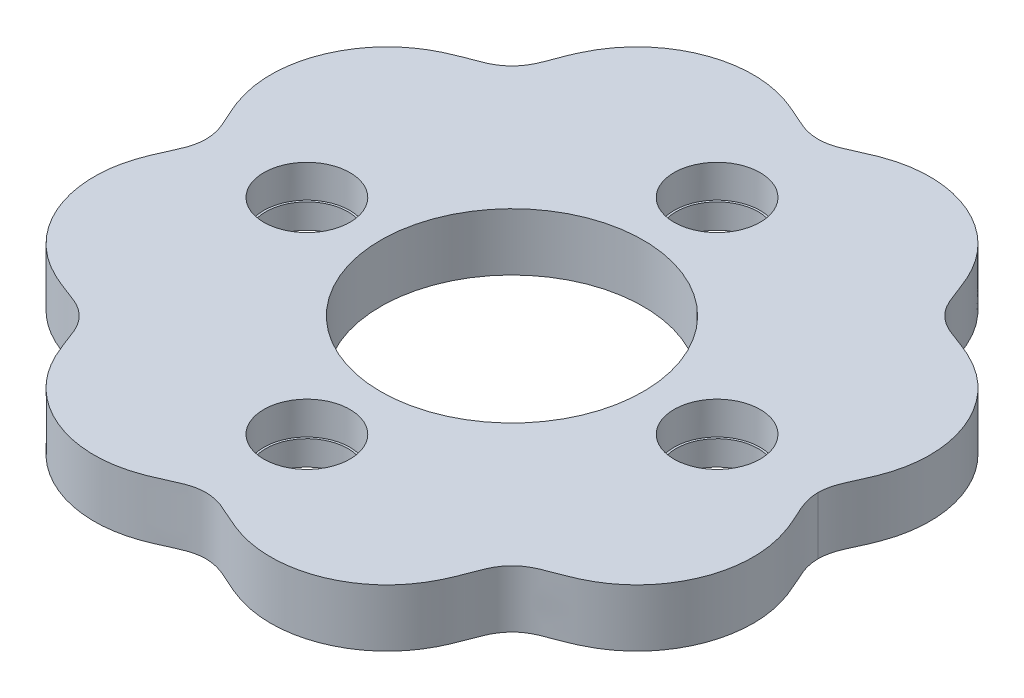
SolidWorks part; units mm, degrees
material "PET"
ref_plane "Front Plane" through (0, 0, 0) normal (0, 0, 1) x (1, 0, 0)
ref_plane "Top Plane" through (0, 0, 0) normal (0, 1, 0) x (1, 0, 0)
ref_plane "Right Plane" through (0, 0, 0) normal (1, 0, 0) x (0, 0, -1)
sketch "Sketch2" plane through (0, 0, 0) normal (0, 1, 0) x (1, 0, 0)
  line L0 (-37.5, 0) -> (37.5, 0) construction
  spline S0 degree 4 poles (36.9805, 20.0285) (37.2753, 19.6778) (37.8347, 18.9513) (38.4555, 17.9854) (39.0737, 16.7557) (39.5005, 15.6923) (39.7876, 14.8217) (40.0191, 13.9346) (40.1939, 13.0347) (40.3111, 12.1255) (40.3698, 11.2106) (40.3695, 10.2938) (40.3175, 9.4934) (40.2359, 8.8108) (40.1529, 8.3024) (40.0885, 7.9647) (40.0287, 7.6841) (39.9777, 7.4611) (39.9238, 7.2412) (39.8664, 7.0219) (39.8025, 6.7937) (39.7309, 6.5533) (39.6637, 6.3374) (39.6136, 6.1836) (39.5479, 5.991) (39.4755, 5.7851) (39.4027, 5.5855) (39.3311, 5.3965) (39.2407, 5.1663) (39.1279, 4.8896) (38.9903, 4.5651) (38.8283, 4.1989) (38.6621, 3.8341) (38.4352, 3.3438) (38.1502, 2.7272) (37.8212, 1.946) (37.5468, 0.9653) (37.4535, -0.0911) (37.5698, -1.0461) (37.7995, -1.8451) (38.0553, -2.5006) (38.2844, -3.0188) (38.5476, -3.5861) (38.8343, -4.2072) (39.213, -5.0714) (39.6429, -6.1955) (40.0348, -7.5456) (40.3091, -9.1291) (40.4025, -10.7334) (40.2923, -12.7392) (39.8007, -15.1154) (38.875, -17.3723) (37.5505, -19.4168) (36.2019, -20.9371) (34.9913, -22.0223) (33.6644, -22.9618) (32.4189, -23.6484) (31.3072, -24.1448) (30.4154, -24.4925) (29.7608, -24.7333) (29.1593, -24.9537) (28.6152, -25.1661) (27.9682, -25.4558) (27.2425, -25.8692) (26.4868, -26.4785) (25.7889, -27.3386) (25.3334, -28.1996) (25.0208, -28.9789) (24.7562, -29.6972) (24.5201, -30.3421) (24.1768, -31.23) (23.6857, -32.344) (23.006, -33.5933) (22.0744, -34.9257) (20.9963, -36.1426) (19.484, -37.5001) (17.4364, -38.8435) (15.1658, -39.787) (12.7656, -40.2907) (10.7279, -40.4037) (9.0981, -40.3067) (7.4903, -40.0231) (6.1205, -39.6185) (4.9809, -39.1759) (3.9811, -38.7332) (3.1077, -38.3232) (2.1628, -37.8962) (1.1027, -37.5687) (0, -37.4517) (-1.1027, -37.5687) (-2.1628, -37.8962) (-3.1077, -38.3232) (-3.9811, -38.7332) (-4.9809, -39.1759) (-6.1205, -39.6185) (-7.4903, -40.0231) (-9.0981, -40.3067) (-10.7279, -40.4037) (-12.7656, -40.2907) (-15.1658, -39.787) (-17.4364, -38.8435) (-19.484, -37.5001) (-20.9963, -36.1426) (-22.0744, -34.9257) (-23.006, -33.5933) (-23.6856, -32.3439) (-24.1768, -31.23) (-24.5707, -30.2109) (-24.8996, -29.3004) (-25.2674, -28.3245) (-25.7889, -27.3386) (-26.4868, -26.4785) (-27.2424, -25.8692) (-27.9682, -25.4558) (-28.6151, -25.166) (-29.1593, -24.9537) (-29.7608, -24.7333) (-30.4154, -24.4925) (-31.3072, -24.1448) (-32.4189, -23.6484) (-33.6644, -22.9618) (-34.9913, -22.0223) (-36.2019, -20.9371) (-37.5505, -19.4168) (-38.875, -17.3723) (-39.8007, -15.1154) (-40.2923, -12.7392) (-40.4025, -10.7334) (-40.3091, -9.1291) (-40.0348, -7.5456) (-39.6429, -6.1955) (-39.213, -5.0714) (-38.8343, -4.2072) (-38.5476, -3.5861) (-38.2844, -3.0188) (-38.0553, -2.5006) (-37.7995, -1.8451) (-37.5698, -1.0461) (-37.4535, -0.0911) (-37.5468, 0.9653) (-37.8212, 1.946) (-38.1502, 2.7272) (-38.4352, 3.3438) (-38.6621, 3.8341) (-38.8283, 4.1989) (-38.9903, 4.5651) (-39.1279, 4.8896) (-39.2407, 5.1663) (-39.3311, 5.3965) (-39.4027, 5.5855) (-39.4755, 5.7851) (-39.5479, 5.991) (-39.6136, 6.1836) (-39.6637, 6.3374) (-39.7309, 6.5533) (-39.8025, 6.7937) (-39.8664, 7.0219) (-39.9238, 7.2412) (-39.9777, 7.4611) (-40.0287, 7.6841) (-40.0885, 7.9647) (-40.1529, 8.3024) (-40.2359, 8.8108) (-40.3175, 9.4934) (-40.3695, 10.2938) (-40.3698, 11.2106) (-40.3111, 12.1255) (-40.1939, 13.0347) (-40.0191, 13.9346) (-39.7876, 14.8217) (-39.5005, 15.6923) (-39.0737, 16.7557) (-38.4555, 17.9854) (-37.8347, 18.9513) (-37.2753, 19.6778) (-36.9805, 20.0285) knots 0 0 0 0 0 0.010311 0.020621 0.025777 0.030932 0.036087 0.041243 0.046398 0.051553 0.056709 0.061864 0.067019 0.069597 0.072175 0.073463 0.074752 0.076041 0.07733 0.078618 0.079907 0.081196 0.082485 0.083613 0.084741 0.085869 0.086997 0.088125 0.089253 0.091509 0.093765 0.09602 0.098276 0.100532 0.105923 0.111314 0.117336 0.123359 0.129627 0.132815 0.136003 0.139191 0.142379 0.146891 0.151403 0.160427 0.169451 0.178475 0.1875 0.196524 0.214573 0.232831 0.24196 0.251089 0.260218 0.269348 0.278476 0.28304 0.287605 0.29089 0.294176 0.297462 0.300748 0.306838 0.312927 0.319161 0.325494 0.32866 0.331826 0.33639 0.340955 0.350083 0.359212 0.368341 0.37747 0.386599 0.404858 0.423193 0.432361 0.441528 0.450696 0.459863 0.46903 0.473614 0.478197 0.484473 0.490748 0.496943 0.503057 0.509252 0.515527 0.521803 0.526386 0.53097 0.540137 0.549304 0.558472 0.567639 0.576807 0.595142 0.613401 0.62253 0.631659 0.640788 0.649917 0.659045 0.66361 0.668174 0.674506 0.680839 0.687073 0.693162 0.699252 0.702538 0.705824 0.70911 0.712395 0.71696 0.721524 0.730652 0.739782 0.748911 0.75804 0.767169 0.785427 0.803476 0.8125 0.821525 0.830549 0.839573 0.848597 0.853109 0.857621 0.860809 0.863997 0.867185 0.870373 0.876641 0.882664 0.888686 0.894077 0.899468 0.901724 0.90398 0.906235 0.908491 0.910747 0.911875 0.913003 0.914131 0.915259 0.916387 0.917515 0.918804 0.920093 0.921382 0.92267 0.923959 0.925248 0.926537 0.927825 0.930403 0.932981 0.938136 0.943291 0.948447 0.953602 0.958757 0.963913 0.969068 0.974223 0.979379 0.989689 1 1 1 1 1 construction
  spline S1 degree 4 poles (37.5, 0) (37.5, -0.1537) (37.5167, -0.5857) (37.6013, -1.1559) (37.7995, -1.8451) (38.0553, -2.5006) (38.2844, -3.0188) (38.5476, -3.5861) (38.8343, -4.2072) (39.213, -5.0714) (39.6429, -6.1955) (40.0348, -7.5456) (40.3091, -9.1291) (40.4025, -10.7334) (40.2923, -12.7392) (39.8007, -15.1154) (38.875, -17.3723) (37.5505, -19.4168) (36.2019, -20.9371) (34.9913, -22.0223) (33.6644, -22.9618) (32.4189, -23.6484) (31.3072, -24.1448) (30.4154, -24.4925) (29.7608, -24.7333) (29.1593, -24.9537) (28.6152, -25.1661) (27.9682, -25.4558) (27.2425, -25.8692) (26.4868, -26.4785) (25.7889, -27.3386) (25.3334, -28.1996) (25.0208, -28.9789) (24.7562, -29.6972) (24.5201, -30.3421) (24.1768, -31.23) (23.6857, -32.344) (23.006, -33.5933) (22.0744, -34.9257) (20.9963, -36.1426) (19.484, -37.5001) (17.4364, -38.8435) (15.1658, -39.787) (12.7656, -40.2907) (10.7279, -40.4037) (9.0981, -40.3067) (7.4903, -40.0231) (6.1205, -39.6185) (4.9809, -39.1759) (3.9811, -38.7332) (3.1077, -38.3232) (2.1628, -37.8962) (1.1027, -37.5687) (0, -37.4517) (-1.1027, -37.5687) (-2.1628, -37.8962) (-3.1077, -38.3232) (-3.9811, -38.7332) (-4.9809, -39.1759) (-6.1205, -39.6185) (-7.4903, -40.0231) (-9.0981, -40.3067) (-10.7279, -40.4037) (-12.7656, -40.2907) (-15.1658, -39.787) (-17.4364, -38.8435) (-19.484, -37.5001) (-20.9963, -36.1426) (-22.0744, -34.9257) (-23.006, -33.5933) (-23.6856, -32.3439) (-24.1768, -31.23) (-24.5707, -30.2109) (-24.8996, -29.3004) (-25.2674, -28.3245) (-25.7889, -27.3386) (-26.4868, -26.4785) (-27.2424, -25.8692) (-27.9682, -25.4558) (-28.6151, -25.166) (-29.1593, -24.9537) (-29.7608, -24.7333) (-30.4154, -24.4925) (-31.3072, -24.1448) (-32.4189, -23.6484) (-33.6644, -22.9618) (-34.9913, -22.0223) (-36.2019, -20.9371) (-37.5505, -19.4168) (-38.875, -17.3723) (-39.8007, -15.1154) (-40.2923, -12.7392) (-40.4025, -10.7334) (-40.3091, -9.1291) (-40.0348, -7.5456) (-39.6429, -6.1955) (-39.213, -5.0714) (-38.8343, -4.2072) (-38.5476, -3.5861) (-38.2844, -3.0188) (-38.0553, -2.5006) (-37.7995, -1.8451) (-37.6013, -1.1559) (-37.5167, -0.5857) (-37.5, -0.1537) (-37.5, 0) knots 0.119901 0.119901 0.119901 0.119901 0.119901 0.123359 0.129627 0.132815 0.136003 0.139191 0.142379 0.146891 0.151403 0.160427 0.169451 0.178475 0.1875 0.196524 0.214573 0.232831 0.24196 0.251089 0.260218 0.269348 0.278476 0.28304 0.287605 0.29089 0.294176 0.297462 0.300748 0.306838 0.312927 0.319161 0.325494 0.32866 0.331826 0.33639 0.340955 0.350083 0.359212 0.368341 0.37747 0.386599 0.404858 0.423193 0.432361 0.441528 0.450696 0.459863 0.46903 0.473614 0.478197 0.484473 0.490748 0.496943 0.503057 0.509252 0.515527 0.521803 0.526386 0.53097 0.540137 0.549304 0.558472 0.567639 0.576807 0.595142 0.613401 0.62253 0.631659 0.640788 0.649917 0.659045 0.66361 0.668174 0.674506 0.680839 0.687073 0.693162 0.699252 0.702538 0.705824 0.70911 0.712395 0.71696 0.721524 0.730652 0.739782 0.748911 0.75804 0.767169 0.785427 0.803476 0.8125 0.821525 0.830549 0.839573 0.848597 0.853109 0.857621 0.860809 0.863997 0.867185 0.870373 0.876641 0.880099 0.880099 0.880099 0.880099 0.880099
  spline S2 degree 4 poles (37.5, 0) (37.5, 0.1537) (37.5167, 0.5857) (37.6013, 1.1559) (37.7995, 1.8451) (38.0553, 2.5006) (38.2844, 3.0188) (38.5476, 3.5861) (38.8343, 4.2072) (39.213, 5.0714) (39.6429, 6.1955) (40.0348, 7.5456) (40.3091, 9.1291) (40.4025, 10.7334) (40.2923, 12.7392) (39.8007, 15.1154) (38.875, 17.3723) (37.5505, 19.4168) (36.2019, 20.9371) (34.9913, 22.0223) (33.6644, 22.9618) (32.4189, 23.6484) (31.3072, 24.1448) (30.4154, 24.4925) (29.7608, 24.7333) (29.1593, 24.9537) (28.6152, 25.1661) (27.9682, 25.4558) (27.2425, 25.8692) (26.4868, 26.4785) (25.7889, 27.3386) (25.3334, 28.1996) (25.0208, 28.9789) (24.7562, 29.6972) (24.5201, 30.3421) (24.1768, 31.23) (23.6857, 32.344) (23.006, 33.5933) (22.0744, 34.9257) (20.9963, 36.1426) (19.484, 37.5001) (17.4364, 38.8435) (15.1658, 39.787) (12.7656, 40.2907) (10.7279, 40.4037) (9.0981, 40.3067) (7.4903, 40.0231) (6.1205, 39.6185) (4.9809, 39.1759) (3.9811, 38.7332) (3.1077, 38.3232) (2.1628, 37.8962) (1.1027, 37.5687) (0, 37.4517) (-1.1027, 37.5687) (-2.1628, 37.8962) (-3.1077, 38.3232) (-3.9811, 38.7332) (-4.9809, 39.1759) (-6.1205, 39.6185) (-7.4903, 40.0231) (-9.0981, 40.3067) (-10.7279, 40.4037) (-12.7656, 40.2907) (-15.1658, 39.787) (-17.4364, 38.8435) (-19.484, 37.5001) (-20.9963, 36.1426) (-22.0744, 34.9257) (-23.006, 33.5933) (-23.6856, 32.3439) (-24.1768, 31.23) (-24.5707, 30.2109) (-24.8996, 29.3004) (-25.2674, 28.3245) (-25.7889, 27.3386) (-26.4868, 26.4785) (-27.2424, 25.8692) (-27.9682, 25.4558) (-28.6151, 25.166) (-29.1593, 24.9537) (-29.7608, 24.7333) (-30.4154, 24.4925) (-31.3072, 24.1448) (-32.4189, 23.6484) (-33.6644, 22.9618) (-34.9913, 22.0223) (-36.2019, 20.9371) (-37.5505, 19.4168) (-38.875, 17.3723) (-39.8007, 15.1154) (-40.2923, 12.7392) (-40.4025, 10.7334) (-40.3091, 9.1291) (-40.0348, 7.5456) (-39.6429, 6.1955) (-39.213, 5.0714) (-38.8343, 4.2072) (-38.5476, 3.5861) (-38.2844, 3.0188) (-38.0553, 2.5006) (-37.7995, 1.8451) (-37.6013, 1.1559) (-37.5167, 0.5857) (-37.5, 0.1537) (-37.5, 0) knots 0.119901 0.119901 0.119901 0.119901 0.119901 0.123359 0.129627 0.132815 0.136003 0.139191 0.142379 0.146891 0.151403 0.160427 0.169451 0.178475 0.1875 0.196524 0.214573 0.232831 0.24196 0.251089 0.260218 0.269348 0.278476 0.28304 0.287605 0.29089 0.294176 0.297462 0.300748 0.306838 0.312927 0.319161 0.325494 0.32866 0.331826 0.33639 0.340955 0.350083 0.359212 0.368341 0.37747 0.386599 0.404858 0.423193 0.432361 0.441528 0.450696 0.459863 0.46903 0.473614 0.478197 0.484473 0.490748 0.496943 0.503057 0.509252 0.515527 0.521803 0.526386 0.53097 0.540137 0.549304 0.558472 0.567639 0.576807 0.595142 0.613401 0.62253 0.631659 0.640788 0.649917 0.659045 0.66361 0.668174 0.674506 0.680839 0.687073 0.693162 0.699252 0.702538 0.705824 0.70911 0.712395 0.71696 0.721524 0.730652 0.739782 0.748911 0.75804 0.767169 0.785427 0.803476 0.8125 0.821525 0.830549 0.839573 0.848597 0.853109 0.857621 0.860809 0.863997 0.867185 0.870373 0.876641 0.880099 0.880099 0.880099 0.880099 0.880099
extrude "Boss-Extrude1" add sketch "Sketch2" along normal blind 7 contours S2 S1
sketch "Sketch3" plane through (0, 7, 0) normal (0, 1, 0) x (1, 0, 0)
  line L0 (0, 0) -> (37.5, 0) construction
  circle A0 centre (0, 0) radius 16
  circle A1 centre (25, 0) radius 5.25
  circle A3 centre (0, -25) radius 5.25
  circle A4 centre (-25, 0) radius 5.25
  circle A5 centre (0, 25) radius 5.25
  spline S0 degree 4 poles (37.5, 0) (37.5, -0.1537) (37.5167, -0.5857) (37.6013, -1.1559) (37.7995, -1.8451) (38.0553, -2.5006) (38.2844, -3.0188) (38.5476, -3.5861) (38.8343, -4.2072) (39.213, -5.0714) (39.6429, -6.1955) (40.0348, -7.5456) (40.3091, -9.1291) (40.4025, -10.7334) (40.2923, -12.7392) (39.8007, -15.1154) (38.875, -17.3723) (37.5505, -19.4168) (36.2019, -20.9371) (34.9913, -22.0223) (33.6644, -22.9618) (32.4189, -23.6484) (31.3072, -24.1448) (30.4154, -24.4925) (29.7608, -24.7333) (29.1593, -24.9537) (28.6152, -25.1661) (27.9682, -25.4558) (27.2425, -25.8692) (26.4868, -26.4785) (25.7889, -27.3386) (25.3334, -28.1996) (25.0208, -28.9789) (24.7562, -29.6972) (24.5201, -30.3421) (24.1768, -31.23) (23.6857, -32.344) (23.006, -33.5933) (22.0744, -34.9257) (20.9963, -36.1426) (19.484, -37.5001) (17.4364, -38.8435) (15.1658, -39.787) (12.7656, -40.2907) (10.7279, -40.4037) (9.0981, -40.3067) (7.4903, -40.0231) (6.1205, -39.6185) (4.9809, -39.1759) (3.9811, -38.7332) (3.1077, -38.3232) (2.1628, -37.8962) (1.1027, -37.5687) (0, -37.4517) (-1.1027, -37.5687) (-2.1628, -37.8962) (-3.1077, -38.3232) (-3.9811, -38.7332) (-4.9809, -39.1759) (-6.1205, -39.6185) (-7.4903, -40.0231) (-9.0981, -40.3067) (-10.7279, -40.4037) (-12.7656, -40.2907) (-15.1658, -39.787) (-17.4364, -38.8435) (-19.484, -37.5001) (-20.9963, -36.1426) (-22.0744, -34.9257) (-23.006, -33.5933) (-23.6856, -32.3439) (-24.1768, -31.23) (-24.5707, -30.2109) (-24.8996, -29.3004) (-25.2674, -28.3245) (-25.7889, -27.3386) (-26.4868, -26.4785) (-27.2424, -25.8692) (-27.9682, -25.4558) (-28.6151, -25.166) (-29.1593, -24.9537) (-29.7608, -24.7333) (-30.4154, -24.4925) (-31.3072, -24.1448) (-32.4189, -23.6484) (-33.6644, -22.9618) (-34.9913, -22.0223) (-36.2019, -20.9371) (-37.5505, -19.4168) (-38.875, -17.3723) (-39.8007, -15.1154) (-40.2923, -12.7392) (-40.4025, -10.7334) (-40.3091, -9.1291) (-40.0348, -7.5456) (-39.6429, -6.1955) (-39.213, -5.0714) (-38.8343, -4.2072) (-38.5476, -3.5861) (-38.2844, -3.0188) (-38.0553, -2.5006) (-37.7995, -1.8451) (-37.6013, -1.1559) (-37.5167, -0.5857) (-37.5, -0.1537) (-37.5, 0) knots 0.119901 0.119901 0.119901 0.119901 0.119901 0.123359 0.129627 0.132815 0.136003 0.139191 0.142379 0.146891 0.151403 0.160427 0.169451 0.178475 0.1875 0.196524 0.214573 0.232831 0.24196 0.251089 0.260218 0.269348 0.278476 0.28304 0.287605 0.29089 0.294176 0.297462 0.300748 0.306838 0.312927 0.319161 0.325494 0.32866 0.331826 0.33639 0.340955 0.350083 0.359212 0.368341 0.37747 0.386599 0.404858 0.423193 0.432361 0.441528 0.450696 0.459863 0.46903 0.473614 0.478197 0.484473 0.490748 0.496943 0.503057 0.509252 0.515527 0.521803 0.526386 0.53097 0.540137 0.549304 0.558472 0.567639 0.576807 0.595142 0.613401 0.62253 0.631659 0.640788 0.649917 0.659045 0.66361 0.668174 0.674506 0.680839 0.687073 0.693162 0.699252 0.702538 0.705824 0.70911 0.712395 0.71696 0.721524 0.730652 0.739782 0.748911 0.75804 0.767169 0.785427 0.803476 0.8125 0.821525 0.830549 0.839573 0.848597 0.853109 0.857621 0.860809 0.863997 0.867185 0.870373 0.876641 0.880099 0.880099 0.880099 0.880099 0.880099 construction
  point P8 (37.5, 0)
  point P18 (0, 0)
  dimension "D1" = 32
  dimension "D2" = 10.5
  dimension "D4" = 25
  dimension "D5" = 4
extrude "Cut-Extrude1" cut sketch "Sketch3" against normal blind 7
sketch "Sketch4" plane through (0, 0, 0) normal (0, -1, 0) x (1, 0, 0)
  spline S4 degree 3 poles (-2948.3885, 722.0287) (-151.4363, 76.2208) (-29.3122, 22.69) (-37.8533, -2.585) (-38.1471, -3.1952) (-38.7107, -4.4187) (-38.9828, -5.0336) (-39.4508, -6.2882) (-39.648, -6.9276) (-39.8757, -7.9088) (-39.9403, -8.2396) (-40.0461, -8.9088) (-40.0873, -9.2487) (-40.1729, -10.2702) (-40.1796, -10.9476) (-40.0964, -12.2955) (-40.0066, -12.966) (-39.7983, -13.9664) (-39.7162, -14.2999) (-39.5299, -14.9551) (-39.4254, -15.2779) (-39.079, -16.2318) (-38.8042, -16.8488) (-38.1662, -18.0446) (-37.7995, -18.6276) (-36.9951, -19.7223) (-36.557, -20.2365) (-35.6094, -21.1989) (-35.0988, -21.6477) (-34.0068, -22.4733) (-33.4366, -22.8413) (-32.2526, -23.4966) (-31.6381, -23.7828) (-30.6936, -24.1698) (-30.3749, -24.292) (-29.7353, -24.5302) (-29.4141, -24.6459) (-28.7761, -24.8878) (-28.4596, -25.0146) (-27.8419, -25.305) (-27.5385, -25.4704) (-26.9685, -25.8482) (-26.7027, -26.0593) (-26.2122, -26.5296) (-25.9857, -26.7918) (-25.5865, -27.3477) (-25.4133, -27.6409) (-25.1061, -28.2501) (-24.9721, -28.5662) (-24.722, -29.2071) (-24.6047, -29.5314) (-24.366, -30.178) (-24.2449, -30.5004) (-23.862, -31.4579) (-23.58, -32.0828) (-22.9307, -33.2897) (-22.5646, -33.8723) (-21.9447, -34.7109) (-21.7254, -34.9856) (-21.2703, -35.5135) (-21.0341, -35.7676) (-20.2998, -36.5011) (-19.7765, -36.9518) (-18.6627, -37.777) (-18.0672, -38.1536) (-16.8421, -38.8083) (-16.2104, -39.0887) (-15.2346, -39.4401) (-14.9046, -39.5456) (-14.235, -39.7331) (-13.894, -39.8152) (-12.1831, -40.161) (-10.8043, -40.2342) (-9.068, -40.0667) (-8.72, -40.0198) (-8.034, -39.9014) (-7.6946, -39.8297) (-6.6868, -39.5791) (-6.0289, -39.3634) (-4.7349, -38.8569) (-4.0997, -38.5639) (-2.8312, -37.9786) (-2.1955, -37.6898) (-1.1773, -37.4157) (-0.8309, -37.3518) (-0.1388, -37.2909) (0.2091, -37.2929) (0.9087, -37.3638) (1.2541, -37.4328) (1.9235, -37.621) (2.2502, -37.7405) (2.8946, -38.0077) (3.2126, -38.1544) (3.8487, -38.4482) (4.1667, -38.5954) (5.126, -39.018) (5.773, -39.274) (7.0935, -39.6938) (7.7666, -39.859) (8.7979, -40.0311) (9.1453, -40.076) (9.8476, -40.1396) (10.2044, -40.1583) (11.9811, -40.1834) (13.3741, -39.9912) (15.0807, -39.4906) (15.419, -39.3775) (16.0811, -39.1284) (16.4062, -38.9921) (17.364, -38.5485) (17.9792, -38.2067) (18.8662, -37.6232) (19.1571, -37.416) (19.72, -36.9818) (19.9916, -36.7554) (20.7778, -36.0486) (21.2637, -35.5408) (21.9348, -34.7238) (22.1489, -34.4422) (22.5573, -33.8603) (22.7513, -33.5603) (23.2966, -32.6452) (23.6131, -32.0104) (24.035, -31.0305) (24.1671, -30.6994) (24.4207, -30.0336) (24.5422, -29.6985) (24.7899, -29.0303) (24.9163, -28.6973) (25.203, -28.0449) (25.3653, -27.7235) (25.7389, -27.1186) (25.9496, -26.8348) (26.4253, -26.3096) (26.6934, -26.0663) (27.2624, -25.6405) (27.5646, -25.4559) (28.1962, -25.1299) (28.5258, -24.9886) (29.1951, -24.726) (29.5346, -24.6036) (30.211, -24.3537) (30.5481, -24.2267) (31.5472, -23.8241) (32.1968, -23.526) (33.4451, -22.8381) (34.0446, -22.4496) (34.9029, -21.793) (35.1822, -21.5619) (35.7264, -21.0739) (35.9929, -20.8154) (36.7549, -20.0151) (37.2156, -19.4476) (38.0459, -18.2477) (38.4158, -17.6149) (39.0608, -16.2832) (39.3278, -15.6011) (39.7553, -14.2058) (39.9157, -13.4925) (40.0733, -12.3983) (40.1117, -12.0294) (40.1591, -11.2964) (40.1684, -10.9307) (40.1534, -9.836) (40.0865, -9.1093) (39.8999, -8.0241) (39.8229, -7.6619) (39.642, -6.9461) (39.5382, -6.593) (39.1911, -5.5467) (38.9098, -4.8672) (38.4549, -3.8599) (38.2979, -3.5261) (37.9924, -2.8554) (37.8446, -2.5182) (37.5906, -1.8289) (37.4849, -1.4765) (32.6595, 22.6356) (171.7208, 86.8036) (1900.9011, -2345.5194) knots -0.595862 -0.595862 -0.595862 -0.595862 0.015625 0.015625 0.03125 0.03125 0.046875 0.046875 0.0625 0.0625 0.070312 0.070312 0.078125 0.078125 0.09375 0.09375 0.109375 0.109375 0.117187 0.117187 0.125 0.125 0.140625 0.140625 0.15625 0.15625 0.171875 0.171875 0.1875 0.1875 0.203125 0.203125 0.21875 0.21875 0.226562 0.226562 0.234375 0.234375 0.242187 0.242187 0.25 0.25 0.257812 0.257812 0.265625 0.265625 0.273437 0.273437 0.28125 0.28125 0.289062 0.289062 0.296875 0.296875 0.3125 0.3125 0.328125 0.328125 0.335937 0.335937 0.34375 0.34375 0.359375 0.359375 0.375 0.375 0.390625 0.390625 0.398437 0.398437 0.40625 0.40625 0.4375 0.4375 0.445312 0.445312 0.453125 0.453125 0.46875 0.46875 0.484375 0.484375 0.5 0.5 0.507812 0.507812 0.515625 0.515625 0.523437 0.523437 0.53125 0.53125 0.539062 0.539062 0.546875 0.546875 0.5625 0.5625 0.578125 0.578125 0.585937 0.585937 0.59375 0.59375 0.625 0.625 0.632812 0.632812 0.640625 0.640625 0.65625 0.65625 0.664062 0.664062 0.671875 0.671875 0.6875 0.6875 0.695312 0.695312 0.703125 0.703125 0.71875 0.71875 0.726562 0.726562 0.734375 0.734375 0.742187 0.742187 0.75 0.75 0.757812 0.757812 0.765625 0.765625 0.773437 0.773437 0.78125 0.78125 0.789062 0.789062 0.796875 0.796875 0.8125 0.8125 0.828125 0.828125 0.835937 0.835937 0.84375 0.84375 0.859375 0.859375 0.875 0.875 0.890625 0.890625 0.90625 0.90625 0.914062 0.914062 0.921875 0.921875 0.9375 0.9375 0.945312 0.945312 0.953125 0.953125 0.96875 0.96875 0.976562 0.976562 0.984375 0.984375 0.992187 0.992187 1.5015 1.5015 1.5015 1.5015 only from (-37.3, 0) to (37.3, 0)
  spline S5 degree 3 poles (2959.6942, -674.8836) (159.4413, -76.6329) (29.2837, -23.2287) (37.8317, 2.5321) (38.1169, 3.1309) (38.67, 4.3291) (38.9391, 4.9306) (39.406, 6.1564) (39.605, 6.7803) (39.9166, 8.056) (40.0298, 8.7075) (40.1293, 9.7073) (40.1505, 10.0435) (40.1686, 10.7108) (40.1657, 11.0433) (40.1219, 12.0378) (40.046, 12.6965) (39.8009, 14.0056) (39.6299, 14.66) (39.2033, 15.9228) (38.9476, 16.535) (38.3524, 17.7213) (38.0116, 18.2974) (36.8656, 19.953) (35.9651, 20.9257) (34.6682, 21.9774) (34.3991, 22.18) (33.8491, 22.5642) (33.5682, 22.7458) (32.7084, 23.2605) (32.1122, 23.5629) (30.8834, 24.1035) (30.2535, 24.3387) (28.9923, 24.8027) (28.3593, 25.0337) (27.173, 25.6725) (26.6404, 26.0718) (25.7322, 27.0751) (25.3881, 27.6463) (24.9705, 28.5655) (24.8471, 28.881) (24.6087, 29.5163) (24.4932, 29.836) (24.1362, 30.7892) (23.8828, 31.4162) (23.0112, 33.2354) (22.2825, 34.3665) (21.1418, 35.6532) (20.9009, 35.9055) (20.4029, 36.3896) (20.1462, 36.621) (19.3542, 37.2845) (18.7968, 37.6859) (17.9172, 38.2274) (17.6167, 38.3978) (17.0008, 38.7178) (16.6853, 38.8674) (15.7319, 39.2776) (15.0821, 39.5029) (13.7545, 39.8588) (13.0763, 39.9895) (11.6925, 40.1507) (11.0033, 40.1794) (9.6304, 40.1362) (8.9466, 40.0641) (7.9251, 39.8793) (7.5841, 39.8046) (6.9111, 39.6316) (6.5788, 39.5334) (5.5932, 39.2068) (4.9518, 38.945) (4.0012, 38.5197) (3.6862, 38.3727) (3.0549, 38.0823) (2.7387, 37.939) (1.7744, 37.5551) (1.1084, 37.3657) (-0.3132, 37.2631) (-1.0098, 37.3537) (-2.3731, 37.7595) (-3.0204, 38.0657) (-4.3192, 38.6656) (-4.971, 38.9584) (-6.3033, 39.4574) (-6.9832, 39.6657) (-8.0287, 39.9006) (-8.3815, 39.9661) (-9.096, 40.0703) (-9.4592, 40.109) (-10.5423, 40.1818) (-11.2606, 40.1739) (-12.6902, 40.0495) (-13.4023, 39.9326) (-14.8151, 39.5876) (-15.4996, 39.3636) (-16.8266, 38.8168) (-17.469, 38.4941) (-18.4002, 37.9335) (-18.7053, 37.7335) (-19.294, 37.3147) (-19.5789, 37.095) (-20.4061, 36.4056) (-20.9207, 35.9057) (-21.636, 35.094) (-21.8657, 34.8121) (-22.3022, 34.2315) (-22.5079, 33.9343) (-23.0891, 33.0233) (-23.428, 32.3894) (-24.0267, 31.0784) (-24.2847, 30.4) (-24.7858, 29.0385) (-25.0297, 28.3549) (-25.5555, 27.397) (-25.7572, 27.0906) (-26.2108, 26.5294) (-26.4639, 26.2717) (-27.0247, 25.8042) (-27.3276, 25.5991) (-27.9582, 25.243) (-28.288, 25.0905) (-28.9629, 24.8128) (-29.3068, 24.687) (-29.9941, 24.4342) (-30.3374, 24.3073) (-31.3574, 23.9062) (-32.0234, 23.6106) (-33.3074, 22.9225) (-33.9261, 22.5314) (-34.8143, 21.8642) (-35.1027, 21.6291) (-35.6549, 21.1411) (-35.9202, 20.8872) (-36.6842, 20.0966) (-37.1512, 19.5312) (-37.7877, 18.6247) (-37.9897, 18.3116) (-38.3661, 17.6752) (-38.5409, 17.3513) (-39.0264, 16.3632) (-39.2984, 15.6825) (-39.7376, 14.2767) (-39.9046, 13.5479) (-40.12, 12.094) (-40.1708, 11.3634) (-40.1608, 10.2619) (-40.143, 9.8938) (-40.0776, 9.1558) (-40.03, 8.7868) (-39.8455, 7.6961) (-39.6659, 6.9845) (-39.2071, 5.5888) (-38.9258, 4.9045) (-38.4691, 3.8906) (-38.3112, 3.5547) (-38.0034, 2.8801) (-37.8539, 2.541) (-37.5965, 1.8472) (-37.4888, 1.4922) (-32.8287, -21.543) (-158.5067, -86.2339) (-1787.1655, 2432.1765) knots -0.619767 -0.619767 -0.619767 -0.619767 0.015625 0.015625 0.03125 0.03125 0.046875 0.046875 0.0625 0.0625 0.078125 0.078125 0.085938 0.085938 0.09375 0.09375 0.109375 0.109375 0.125 0.125 0.140625 0.140625 0.15625 0.15625 0.1875 0.1875 0.195313 0.195313 0.203125 0.203125 0.21875 0.21875 0.234375 0.234375 0.25 0.25 0.265625 0.265625 0.28125 0.28125 0.289063 0.289063 0.296875 0.296875 0.3125 0.3125 0.34375 0.34375 0.351563 0.351563 0.359375 0.359375 0.375 0.375 0.382813 0.382813 0.390625 0.390625 0.40625 0.40625 0.421875 0.421875 0.4375 0.4375 0.453125 0.453125 0.460938 0.460938 0.46875 0.46875 0.484375 0.484375 0.492188 0.492188 0.5 0.5 0.515625 0.515625 0.53125 0.53125 0.546875 0.546875 0.5625 0.5625 0.578125 0.578125 0.585938 0.585938 0.59375 0.59375 0.609375 0.609375 0.625 0.625 0.640625 0.640625 0.65625 0.65625 0.664063 0.664063 0.671875 0.671875 0.6875 0.6875 0.695313 0.695313 0.703125 0.703125 0.71875 0.71875 0.734375 0.734375 0.75 0.75 0.757813 0.757813 0.765625 0.765625 0.773438 0.773438 0.78125 0.78125 0.789063 0.789063 0.796875 0.796875 0.8125 0.8125 0.828125 0.828125 0.835938 0.835938 0.84375 0.84375 0.859375 0.859375 0.867188 0.867188 0.875 0.875 0.890625 0.890625 0.90625 0.90625 0.921875 0.921875 0.929688 0.929688 0.9375 0.9375 0.953125 0.953125 0.96875 0.96875 0.976563 0.976563 0.984375 0.984375 0.992188 0.992188 1.473972 1.473972 1.473972 1.473972 only from (37.3, 0) to (-37.3, 0)
  spline S6 degree 3 poles (-37.3, 0) (-37.3, -0.6769) (-37.4276, -1.3255) (-37.8533, -2.585) (-38.1471, -3.1952) (-38.7107, -4.4187) (-38.9828, -5.0336) (-39.4508, -6.2882) (-39.648, -6.9276) (-39.8757, -7.9088) (-39.9403, -8.2396) (-40.0461, -8.9088) (-40.0873, -9.2487) (-40.1729, -10.2702) (-40.1796, -10.9476) (-40.0964, -12.2955) (-40.0066, -12.966) (-39.7983, -13.9664) (-39.7162, -14.2999) (-39.5299, -14.9551) (-39.4254, -15.2779) (-39.079, -16.2318) (-38.8042, -16.8488) (-38.1662, -18.0446) (-37.7995, -18.6276) (-36.9951, -19.7223) (-36.557, -20.2365) (-35.6094, -21.1989) (-35.0988, -21.6477) (-34.0068, -22.4733) (-33.4366, -22.8413) (-32.2526, -23.4966) (-31.6381, -23.7828) (-30.6936, -24.1698) (-30.3749, -24.292) (-29.7353, -24.5302) (-29.4141, -24.6459) (-28.7761, -24.8878) (-28.4596, -25.0146) (-27.8419, -25.305) (-27.5385, -25.4704) (-26.9685, -25.8482) (-26.7027, -26.0593) (-26.2122, -26.5296) (-25.9857, -26.7918) (-25.5865, -27.3477) (-25.4133, -27.6409) (-25.1061, -28.2501) (-24.9721, -28.5662) (-24.722, -29.2071) (-24.6047, -29.5314) (-24.366, -30.178) (-24.2449, -30.5004) (-23.862, -31.4579) (-23.58, -32.0828) (-22.9307, -33.2897) (-22.5646, -33.8723) (-21.9447, -34.7109) (-21.7254, -34.9856) (-21.2703, -35.5135) (-21.0341, -35.7676) (-20.2998, -36.5011) (-19.7765, -36.9518) (-18.6627, -37.777) (-18.0672, -38.1536) (-16.8421, -38.8083) (-16.2104, -39.0887) (-15.2346, -39.4401) (-14.9046, -39.5456) (-14.235, -39.7331) (-13.894, -39.8152) (-12.1831, -40.161) (-10.8043, -40.2342) (-9.068, -40.0667) (-8.72, -40.0198) (-8.034, -39.9014) (-7.6946, -39.8297) (-6.6868, -39.5791) (-6.0289, -39.3634) (-4.7349, -38.8569) (-4.0997, -38.5639) (-2.8312, -37.9786) (-2.1955, -37.6898) (-1.1773, -37.4157) (-0.8309, -37.3518) (-0.1388, -37.2909) (0.2091, -37.2929) (0.9087, -37.3638) (1.2541, -37.4328) (1.9235, -37.621) (2.2502, -37.7405) (2.8946, -38.0077) (3.2126, -38.1544) (3.8487, -38.4482) (4.1667, -38.5954) (5.126, -39.018) (5.773, -39.274) (7.0935, -39.6938) (7.7666, -39.859) (8.7979, -40.0311) (9.1453, -40.076) (9.8476, -40.1396) (10.2044, -40.1583) (11.9811, -40.1834) (13.3741, -39.9912) (15.0807, -39.4906) (15.419, -39.3775) (16.0811, -39.1284) (16.4062, -38.9921) (17.364, -38.5485) (17.9792, -38.2067) (18.8662, -37.6232) (19.1571, -37.416) (19.72, -36.9818) (19.9916, -36.7554) (20.7778, -36.0486) (21.2637, -35.5408) (21.9348, -34.7238) (22.1489, -34.4422) (22.5573, -33.8603) (22.7513, -33.5603) (23.2966, -32.6452) (23.6131, -32.0104) (24.035, -31.0305) (24.1671, -30.6994) (24.4207, -30.0336) (24.5422, -29.6985) (24.7899, -29.0303) (24.9163, -28.6973) (25.203, -28.0449) (25.3653, -27.7235) (25.7389, -27.1186) (25.9496, -26.8348) (26.4253, -26.3096) (26.6934, -26.0663) (27.2624, -25.6405) (27.5646, -25.4559) (28.1962, -25.1299) (28.5258, -24.9886) (29.1951, -24.726) (29.5346, -24.6036) (30.211, -24.3537) (30.5481, -24.2267) (31.5472, -23.8241) (32.1968, -23.526) (33.4451, -22.8381) (34.0446, -22.4496) (34.9029, -21.793) (35.1822, -21.5619) (35.7264, -21.0739) (35.9929, -20.8154) (36.7549, -20.0151) (37.2156, -19.4476) (38.0459, -18.2477) (38.4158, -17.6149) (39.0608, -16.2832) (39.3278, -15.6011) (39.7553, -14.2058) (39.9157, -13.4925) (40.0733, -12.3983) (40.1117, -12.0294) (40.1591, -11.2964) (40.1684, -10.9307) (40.1534, -9.836) (40.0865, -9.1093) (39.8999, -8.0241) (39.8229, -7.6619) (39.642, -6.9461) (39.5382, -6.593) (39.1911, -5.5467) (38.9098, -4.8672) (38.4549, -3.8599) (38.2979, -3.5261) (37.9924, -2.8554) (37.8446, -2.5182) (37.5906, -1.8289) (37.4849, -1.4765) (37.3391, -0.7479) (37.3, -0.3741) (37.3, 0) knots 0 0 0 0 0.015625 0.015625 0.03125 0.03125 0.046875 0.046875 0.0625 0.0625 0.070312 0.070312 0.078125 0.078125 0.09375 0.09375 0.109375 0.109375 0.117187 0.117187 0.125 0.125 0.140625 0.140625 0.15625 0.15625 0.171875 0.171875 0.1875 0.1875 0.203125 0.203125 0.21875 0.21875 0.226562 0.226562 0.234375 0.234375 0.242187 0.242187 0.25 0.25 0.257812 0.257812 0.265625 0.265625 0.273437 0.273437 0.28125 0.28125 0.289062 0.289062 0.296875 0.296875 0.3125 0.3125 0.328125 0.328125 0.335937 0.335937 0.34375 0.34375 0.359375 0.359375 0.375 0.375 0.390625 0.390625 0.398437 0.398437 0.40625 0.40625 0.4375 0.4375 0.445312 0.445312 0.453125 0.453125 0.46875 0.46875 0.484375 0.484375 0.5 0.5 0.507812 0.507812 0.515625 0.515625 0.523437 0.523437 0.53125 0.53125 0.539062 0.539062 0.546875 0.546875 0.5625 0.5625 0.578125 0.578125 0.585937 0.585937 0.59375 0.59375 0.625 0.625 0.632812 0.632812 0.640625 0.640625 0.65625 0.65625 0.664062 0.664062 0.671875 0.671875 0.6875 0.6875 0.695312 0.695312 0.703125 0.703125 0.71875 0.71875 0.726562 0.726562 0.734375 0.734375 0.742187 0.742187 0.75 0.75 0.757812 0.757812 0.765625 0.765625 0.773437 0.773437 0.78125 0.78125 0.789062 0.789062 0.796875 0.796875 0.8125 0.8125 0.828125 0.828125 0.835937 0.835937 0.84375 0.84375 0.859375 0.859375 0.875 0.875 0.890625 0.890625 0.90625 0.90625 0.914062 0.914062 0.921875 0.921875 0.9375 0.9375 0.945312 0.945312 0.953125 0.953125 0.96875 0.96875 0.976562 0.976562 0.984375 0.984375 0.992187 0.992187 1 1 1 1
  spline S7 degree 3 poles (37.3, 0) (37.3, 0.6601) (37.4214, 1.2955) (37.8317, 2.5321) (38.1169, 3.1309) (38.67, 4.3291) (38.9391, 4.9306) (39.406, 6.1564) (39.605, 6.7803) (39.9166, 8.056) (40.0298, 8.7075) (40.1293, 9.7073) (40.1505, 10.0435) (40.1686, 10.7108) (40.1657, 11.0433) (40.1219, 12.0378) (40.046, 12.6965) (39.8009, 14.0056) (39.6299, 14.66) (39.2033, 15.9228) (38.9476, 16.535) (38.3524, 17.7213) (38.0116, 18.2974) (36.8656, 19.953) (35.9651, 20.9257) (34.6682, 21.9774) (34.3991, 22.18) (33.8491, 22.5642) (33.5682, 22.7458) (32.7084, 23.2605) (32.1122, 23.5629) (30.8834, 24.1035) (30.2535, 24.3387) (28.9923, 24.8027) (28.3593, 25.0337) (27.173, 25.6725) (26.6404, 26.0718) (25.7322, 27.0751) (25.3881, 27.6463) (24.9705, 28.5655) (24.8471, 28.881) (24.6087, 29.5163) (24.4932, 29.836) (24.1362, 30.7892) (23.8828, 31.4162) (23.0112, 33.2354) (22.2825, 34.3665) (21.1418, 35.6532) (20.9009, 35.9055) (20.4029, 36.3896) (20.1462, 36.621) (19.3542, 37.2845) (18.7968, 37.6859) (17.9172, 38.2274) (17.6167, 38.3978) (17.0008, 38.7178) (16.6853, 38.8674) (15.7319, 39.2776) (15.0821, 39.5029) (13.7545, 39.8588) (13.0763, 39.9895) (11.6925, 40.1507) (11.0033, 40.1794) (9.6304, 40.1362) (8.9466, 40.0641) (7.9251, 39.8793) (7.5841, 39.8046) (6.9111, 39.6316) (6.5788, 39.5334) (5.5932, 39.2068) (4.9518, 38.945) (4.0012, 38.5197) (3.6862, 38.3727) (3.0549, 38.0823) (2.7387, 37.939) (1.7744, 37.5551) (1.1084, 37.3657) (-0.3132, 37.2631) (-1.0098, 37.3537) (-2.3731, 37.7595) (-3.0204, 38.0657) (-4.3192, 38.6656) (-4.971, 38.9584) (-6.3033, 39.4574) (-6.9832, 39.6657) (-8.0287, 39.9006) (-8.3815, 39.9661) (-9.096, 40.0703) (-9.4592, 40.109) (-10.5423, 40.1818) (-11.2606, 40.1739) (-12.6902, 40.0495) (-13.4023, 39.9326) (-14.8151, 39.5876) (-15.4996, 39.3636) (-16.8266, 38.8168) (-17.469, 38.4941) (-18.4002, 37.9335) (-18.7053, 37.7335) (-19.294, 37.3147) (-19.5789, 37.095) (-20.4061, 36.4056) (-20.9207, 35.9057) (-21.636, 35.094) (-21.8657, 34.8121) (-22.3022, 34.2315) (-22.5079, 33.9343) (-23.0891, 33.0233) (-23.428, 32.3894) (-24.0267, 31.0784) (-24.2847, 30.4) (-24.7858, 29.0385) (-25.0297, 28.3549) (-25.5555, 27.397) (-25.7572, 27.0906) (-26.2108, 26.5294) (-26.4639, 26.2717) (-27.0247, 25.8042) (-27.3276, 25.5991) (-27.9582, 25.243) (-28.288, 25.0905) (-28.9629, 24.8128) (-29.3068, 24.687) (-29.9941, 24.4342) (-30.3374, 24.3073) (-31.3574, 23.9062) (-32.0234, 23.6106) (-33.3074, 22.9225) (-33.9261, 22.5314) (-34.8143, 21.8642) (-35.1027, 21.6291) (-35.6549, 21.1411) (-35.9202, 20.8872) (-36.6842, 20.0966) (-37.1512, 19.5312) (-37.7877, 18.6247) (-37.9897, 18.3116) (-38.3661, 17.6752) (-38.5409, 17.3513) (-39.0264, 16.3632) (-39.2984, 15.6825) (-39.7376, 14.2767) (-39.9046, 13.5479) (-40.12, 12.094) (-40.1708, 11.3634) (-40.1608, 10.2619) (-40.143, 9.8938) (-40.0776, 9.1558) (-40.03, 8.7868) (-39.8455, 7.6961) (-39.6659, 6.9845) (-39.2071, 5.5888) (-38.9258, 4.9045) (-38.4691, 3.8906) (-38.3112, 3.5547) (-38.0034, 2.8801) (-37.8539, 2.541) (-37.5965, 1.8472) (-37.4888, 1.4922) (-37.3401, 0.7571) (-37.3, 0.3785) (-37.3, 0) knots 0 0 0 0 0.015625 0.015625 0.03125 0.03125 0.046875 0.046875 0.0625 0.0625 0.078125 0.078125 0.085938 0.085938 0.09375 0.09375 0.109375 0.109375 0.125 0.125 0.140625 0.140625 0.15625 0.15625 0.1875 0.1875 0.195313 0.195313 0.203125 0.203125 0.21875 0.21875 0.234375 0.234375 0.25 0.25 0.265625 0.265625 0.28125 0.28125 0.289063 0.289063 0.296875 0.296875 0.3125 0.3125 0.34375 0.34375 0.351563 0.351563 0.359375 0.359375 0.375 0.375 0.382813 0.382813 0.390625 0.390625 0.40625 0.40625 0.421875 0.421875 0.4375 0.4375 0.453125 0.453125 0.460938 0.460938 0.46875 0.46875 0.484375 0.484375 0.492188 0.492188 0.5 0.5 0.515625 0.515625 0.53125 0.53125 0.546875 0.546875 0.5625 0.5625 0.578125 0.578125 0.585938 0.585938 0.59375 0.59375 0.609375 0.609375 0.625 0.625 0.640625 0.640625 0.65625 0.65625 0.664063 0.664063 0.671875 0.671875 0.6875 0.6875 0.695313 0.695313 0.703125 0.703125 0.71875 0.71875 0.734375 0.734375 0.75 0.75 0.757813 0.757813 0.765625 0.765625 0.773438 0.773438 0.78125 0.78125 0.789063 0.789063 0.796875 0.796875 0.8125 0.8125 0.828125 0.828125 0.835938 0.835938 0.84375 0.84375 0.859375 0.859375 0.867188 0.867188 0.875 0.875 0.890625 0.890625 0.90625 0.90625 0.921875 0.921875 0.929688 0.929688 0.9375 0.9375 0.953125 0.953125 0.96875 0.96875 0.976563 0.976563 0.984375 0.984375 0.992188 0.992188 1 1 1 1
  spline S9 degree 4 poles (-2927.7566, 450.1538) (154.1429, 42.4244) (54.7666, -22.8241) (34.992, -7.9225) (37.7995, 1.8451) (38.0553, 2.5006) (38.2844, 3.0188) (38.5476, 3.5861) (38.8343, 4.2072) (39.213, 5.0714) (39.6429, 6.1955) (40.0348, 7.5456) (40.3091, 9.1291) (40.4025, 10.7334) (40.2923, 12.7392) (39.8007, 15.1154) (38.875, 17.3723) (37.5505, 19.4168) (36.2019, 20.9371) (34.9913, 22.0223) (33.6644, 22.9618) (32.4189, 23.6484) (31.3072, 24.1448) (30.4154, 24.4925) (29.7608, 24.7333) (29.1593, 24.9537) (28.6152, 25.1661) (27.9682, 25.4558) (27.2425, 25.8692) (26.4868, 26.4785) (25.7889, 27.3386) (25.3334, 28.1996) (25.0208, 28.9789) (24.7562, 29.6972) (24.5201, 30.3421) (24.1768, 31.23) (23.6857, 32.344) (23.006, 33.5933) (22.0744, 34.9257) (20.9963, 36.1426) (19.484, 37.5001) (17.4364, 38.8435) (15.1658, 39.787) (12.7656, 40.2907) (10.7279, 40.4037) (9.0981, 40.3067) (7.4903, 40.0231) (6.1205, 39.6185) (4.9809, 39.1759) (3.9811, 38.7332) (3.1077, 38.3232) (2.1628, 37.8962) (1.1027, 37.5687) (0, 37.4517) (-1.1027, 37.5687) (-2.1628, 37.8962) (-3.1077, 38.3232) (-3.9811, 38.7332) (-4.9809, 39.1759) (-6.1205, 39.6185) (-7.4903, 40.0231) (-9.0981, 40.3067) (-10.7279, 40.4037) (-12.7656, 40.2907) (-15.1658, 39.787) (-17.4364, 38.8435) (-19.484, 37.5001) (-20.9963, 36.1426) (-22.0744, 34.9257) (-23.006, 33.5933) (-23.6856, 32.3439) (-24.1768, 31.23) (-24.5707, 30.2109) (-24.8996, 29.3004) (-25.2674, 28.3245) (-25.7889, 27.3386) (-26.4868, 26.4785) (-27.2424, 25.8692) (-27.9682, 25.4558) (-28.6151, 25.166) (-29.1593, 24.9537) (-29.7608, 24.7333) (-30.4154, 24.4925) (-31.3072, 24.1448) (-32.4189, 23.6484) (-33.6644, 22.9618) (-34.9913, 22.0223) (-36.2019, 20.9371) (-37.5505, 19.4168) (-38.875, 17.3723) (-39.8007, 15.1154) (-40.2923, 12.7392) (-40.4025, 10.7334) (-40.3091, 9.1291) (-40.0348, 7.5456) (-39.6429, 6.1955) (-39.213, 5.0714) (-38.8343, 4.2072) (-38.5476, 3.5861) (-38.2844, 3.0188) (-38.0553, 2.5006) (-37.7995, 1.8451) (-34.992, -7.9224) (-54.7661, -22.8237) (-154.1395, 42.4222) (2927.615, 450.1351) knots -0.092193 -0.092193 -0.092193 -0.092193 -0.092193 0.123359 0.129627 0.132815 0.136003 0.139191 0.142379 0.146891 0.151403 0.160427 0.169451 0.178475 0.1875 0.196524 0.214573 0.232831 0.24196 0.251089 0.260218 0.269348 0.278476 0.28304 0.287605 0.29089 0.294176 0.297462 0.300748 0.306838 0.312927 0.319161 0.325494 0.32866 0.331826 0.33639 0.340955 0.350083 0.359212 0.368341 0.37747 0.386599 0.404858 0.423193 0.432361 0.441528 0.450696 0.459863 0.46903 0.473614 0.478197 0.484473 0.490748 0.496943 0.503057 0.509252 0.515527 0.521803 0.526386 0.53097 0.540137 0.549304 0.558472 0.567639 0.576807 0.595142 0.613401 0.62253 0.631659 0.640788 0.649917 0.659045 0.66361 0.668174 0.674506 0.680839 0.687073 0.693162 0.699252 0.702538 0.705824 0.70911 0.712395 0.71696 0.721524 0.730652 0.739782 0.748911 0.75804 0.767169 0.785427 0.803476 0.8125 0.821525 0.830549 0.839573 0.848597 0.853109 0.857621 0.860809 0.863997 0.867185 0.870373 0.876641 1.09219 1.09219 1.09219 1.09219 1.09219 only from (37.5, 0) to (-37.5, 0)
  spline S10 degree 4 poles (2927.7566, -450.1538) (-154.1429, -42.4244) (-54.7666, 22.8241) (-34.992, 7.9225) (-37.7995, -1.8451) (-38.0553, -2.5006) (-38.2844, -3.0188) (-38.5476, -3.5861) (-38.8343, -4.2072) (-39.213, -5.0714) (-39.6429, -6.1955) (-40.0348, -7.5456) (-40.3091, -9.1291) (-40.4025, -10.7334) (-40.2923, -12.7392) (-39.8007, -15.1154) (-38.875, -17.3723) (-37.5505, -19.4168) (-36.2019, -20.9371) (-34.9913, -22.0223) (-33.6644, -22.9618) (-32.4189, -23.6484) (-31.3072, -24.1448) (-30.4154, -24.4925) (-29.7608, -24.7333) (-29.1593, -24.9537) (-28.6151, -25.166) (-27.9682, -25.4558) (-27.2424, -25.8692) (-26.4868, -26.4785) (-25.7889, -27.3386) (-25.2674, -28.3245) (-24.8996, -29.3004) (-24.5707, -30.2109) (-24.1768, -31.23) (-23.6856, -32.3439) (-23.006, -33.5933) (-22.0744, -34.9257) (-20.9963, -36.1426) (-19.484, -37.5001) (-17.4364, -38.8435) (-15.1658, -39.787) (-12.7656, -40.2907) (-10.7279, -40.4037) (-9.0981, -40.3067) (-7.4903, -40.0231) (-6.1205, -39.6185) (-4.9809, -39.1759) (-3.9811, -38.7332) (-3.1077, -38.3232) (-2.1628, -37.8962) (-1.1027, -37.5687) (0, -37.4517) (1.1027, -37.5687) (2.1628, -37.8962) (3.1077, -38.3232) (3.9811, -38.7332) (4.9809, -39.1759) (6.1205, -39.6185) (7.4903, -40.0231) (9.0981, -40.3067) (10.7279, -40.4037) (12.7656, -40.2907) (15.1658, -39.787) (17.4364, -38.8435) (19.484, -37.5001) (20.9963, -36.1426) (22.0744, -34.9257) (23.006, -33.5933) (23.6857, -32.344) (24.1768, -31.23) (24.5201, -30.3421) (24.7562, -29.6972) (25.0208, -28.9789) (25.3334, -28.1996) (25.7889, -27.3386) (26.4868, -26.4785) (27.2425, -25.8692) (27.9682, -25.4558) (28.6152, -25.1661) (29.1593, -24.9537) (29.7608, -24.7333) (30.4154, -24.4925) (31.3072, -24.1448) (32.4189, -23.6484) (33.6644, -22.9618) (34.9913, -22.0223) (36.2019, -20.9371) (37.5505, -19.4168) (38.875, -17.3723) (39.8007, -15.1154) (40.2923, -12.7392) (40.4025, -10.7334) (40.3091, -9.1291) (40.0348, -7.5456) (39.6429, -6.1955) (39.213, -5.0714) (38.8343, -4.2072) (38.5476, -3.5861) (38.2844, -3.0188) (38.0553, -2.5006) (37.7995, -1.8451) (34.992, 7.9224) (54.7661, 22.8237) (154.1395, -42.4222) (-2927.615, -450.1351) knots -0.092193 -0.092193 -0.092193 -0.092193 -0.092193 0.123359 0.129627 0.132815 0.136003 0.139191 0.142379 0.146891 0.151403 0.160427 0.169451 0.178475 0.1875 0.196524 0.214573 0.232831 0.24196 0.251089 0.260218 0.269348 0.278476 0.28304 0.287605 0.29089 0.294176 0.297462 0.300748 0.306838 0.312927 0.319161 0.325494 0.331826 0.33639 0.340955 0.350083 0.359212 0.368341 0.37747 0.386599 0.404858 0.423193 0.432361 0.441528 0.450696 0.459863 0.46903 0.473614 0.478197 0.484473 0.490748 0.496943 0.503057 0.509252 0.515527 0.521803 0.526386 0.53097 0.540137 0.549304 0.558472 0.567639 0.576807 0.595142 0.613401 0.62253 0.631659 0.640788 0.649917 0.659045 0.66361 0.668174 0.67134 0.674506 0.680839 0.687073 0.693162 0.699252 0.702538 0.705824 0.70911 0.712395 0.71696 0.721524 0.730652 0.739782 0.748911 0.75804 0.767169 0.785427 0.803476 0.8125 0.821525 0.830549 0.839573 0.848597 0.853109 0.857621 0.860809 0.863997 0.867185 0.870373 0.876641 1.09219 1.09219 1.09219 1.09219 1.09219 only from (-37.5, 0) to (37.5, 0)
  spline S11 degree 4 poles (37.5, 0) (37.5, 0.1537) (37.5167, 0.5857) (37.6013, 1.1559) (37.7995, 1.8451) (38.0553, 2.5006) (38.2844, 3.0188) (38.5476, 3.5861) (38.8343, 4.2072) (39.213, 5.0714) (39.6429, 6.1955) (40.0348, 7.5456) (40.3091, 9.1291) (40.4025, 10.7334) (40.2923, 12.7392) (39.8007, 15.1154) (38.875, 17.3723) (37.5505, 19.4168) (36.2019, 20.9371) (34.9913, 22.0223) (33.6644, 22.9618) (32.4189, 23.6484) (31.3072, 24.1448) (30.4154, 24.4925) (29.7608, 24.7333) (29.1593, 24.9537) (28.6152, 25.1661) (27.9682, 25.4558) (27.2425, 25.8692) (26.4868, 26.4785) (25.7889, 27.3386) (25.3334, 28.1996) (25.0208, 28.9789) (24.7562, 29.6972) (24.5201, 30.3421) (24.1768, 31.23) (23.6857, 32.344) (23.006, 33.5933) (22.0744, 34.9257) (20.9963, 36.1426) (19.484, 37.5001) (17.4364, 38.8435) (15.1658, 39.787) (12.7656, 40.2907) (10.7279, 40.4037) (9.0981, 40.3067) (7.4903, 40.0231) (6.1205, 39.6185) (4.9809, 39.1759) (3.9811, 38.7332) (3.1077, 38.3232) (2.1628, 37.8962) (1.1027, 37.5687) (0, 37.4517) (-1.1027, 37.5687) (-2.1628, 37.8962) (-3.1077, 38.3232) (-3.9811, 38.7332) (-4.9809, 39.1759) (-6.1205, 39.6185) (-7.4903, 40.0231) (-9.0981, 40.3067) (-10.7279, 40.4037) (-12.7656, 40.2907) (-15.1658, 39.787) (-17.4364, 38.8435) (-19.484, 37.5001) (-20.9963, 36.1426) (-22.0744, 34.9257) (-23.006, 33.5933) (-23.6856, 32.3439) (-24.1768, 31.23) (-24.5707, 30.2109) (-24.8996, 29.3004) (-25.2674, 28.3245) (-25.7889, 27.3386) (-26.4868, 26.4785) (-27.2424, 25.8692) (-27.9682, 25.4558) (-28.6151, 25.166) (-29.1593, 24.9537) (-29.7608, 24.7333) (-30.4154, 24.4925) (-31.3072, 24.1448) (-32.4189, 23.6484) (-33.6644, 22.9618) (-34.9913, 22.0223) (-36.2019, 20.9371) (-37.5505, 19.4168) (-38.875, 17.3723) (-39.8007, 15.1154) (-40.2923, 12.7392) (-40.4025, 10.7334) (-40.3091, 9.1291) (-40.0348, 7.5456) (-39.6429, 6.1955) (-39.213, 5.0714) (-38.8343, 4.2072) (-38.5476, 3.5861) (-38.2844, 3.0188) (-38.0553, 2.5006) (-37.7995, 1.8451) (-37.6013, 1.1559) (-37.5167, 0.5857) (-37.5, 0.1537) (-37.5, 0) knots 0.119901 0.119901 0.119901 0.119901 0.119901 0.123359 0.129627 0.132815 0.136003 0.139191 0.142379 0.146891 0.151403 0.160427 0.169451 0.178475 0.1875 0.196524 0.214573 0.232831 0.24196 0.251089 0.260218 0.269348 0.278476 0.28304 0.287605 0.29089 0.294176 0.297462 0.300748 0.306838 0.312927 0.319161 0.325494 0.32866 0.331826 0.33639 0.340955 0.350083 0.359212 0.368341 0.37747 0.386599 0.404858 0.423193 0.432361 0.441528 0.450696 0.459863 0.46903 0.473614 0.478197 0.484473 0.490748 0.496943 0.503057 0.509252 0.515527 0.521803 0.526386 0.53097 0.540137 0.549304 0.558472 0.567639 0.576807 0.595142 0.613401 0.62253 0.631659 0.640788 0.649917 0.659045 0.66361 0.668174 0.674506 0.680839 0.687073 0.693162 0.699252 0.702538 0.705824 0.70911 0.712395 0.71696 0.721524 0.730652 0.739782 0.748911 0.75804 0.767169 0.785427 0.803476 0.8125 0.821525 0.830549 0.839573 0.848597 0.853109 0.857621 0.860809 0.863997 0.867185 0.870373 0.876641 0.880099 0.880099 0.880099 0.880099 0.880099
  spline S12 degree 4 poles (-37.5, 0) (-37.5, -0.1537) (-37.5167, -0.5857) (-37.6013, -1.1559) (-37.7995, -1.8451) (-38.0553, -2.5006) (-38.2844, -3.0188) (-38.5476, -3.5861) (-38.8343, -4.2072) (-39.213, -5.0714) (-39.6429, -6.1955) (-40.0348, -7.5456) (-40.3091, -9.1291) (-40.4025, -10.7334) (-40.2923, -12.7392) (-39.8007, -15.1154) (-38.875, -17.3723) (-37.5505, -19.4168) (-36.2019, -20.9371) (-34.9913, -22.0223) (-33.6644, -22.9618) (-32.4189, -23.6484) (-31.3072, -24.1448) (-30.4154, -24.4925) (-29.7608, -24.7333) (-29.1593, -24.9537) (-28.6151, -25.166) (-27.9682, -25.4558) (-27.2424, -25.8692) (-26.4868, -26.4785) (-25.7889, -27.3386) (-25.2674, -28.3245) (-24.8996, -29.3004) (-24.5707, -30.2109) (-24.1768, -31.23) (-23.6856, -32.3439) (-23.006, -33.5933) (-22.0744, -34.9257) (-20.9963, -36.1426) (-19.484, -37.5001) (-17.4364, -38.8435) (-15.1658, -39.787) (-12.7656, -40.2907) (-10.7279, -40.4037) (-9.0981, -40.3067) (-7.4903, -40.0231) (-6.1205, -39.6185) (-4.9809, -39.1759) (-3.9811, -38.7332) (-3.1077, -38.3232) (-2.1628, -37.8962) (-1.1027, -37.5687) (0, -37.4517) (1.1027, -37.5687) (2.1628, -37.8962) (3.1077, -38.3232) (3.9811, -38.7332) (4.9809, -39.1759) (6.1205, -39.6185) (7.4903, -40.0231) (9.0981, -40.3067) (10.7279, -40.4037) (12.7656, -40.2907) (15.1658, -39.787) (17.4364, -38.8435) (19.484, -37.5001) (20.9963, -36.1426) (22.0744, -34.9257) (23.006, -33.5933) (23.6857, -32.344) (24.1768, -31.23) (24.5201, -30.3421) (24.7562, -29.6972) (25.0208, -28.9789) (25.3334, -28.1996) (25.7889, -27.3386) (26.4868, -26.4785) (27.2425, -25.8692) (27.9682, -25.4558) (28.6152, -25.1661) (29.1593, -24.9537) (29.7608, -24.7333) (30.4154, -24.4925) (31.3072, -24.1448) (32.4189, -23.6484) (33.6644, -22.9618) (34.9913, -22.0223) (36.2019, -20.9371) (37.5505, -19.4168) (38.875, -17.3723) (39.8007, -15.1154) (40.2923, -12.7392) (40.4025, -10.7334) (40.3091, -9.1291) (40.0348, -7.5456) (39.6429, -6.1955) (39.213, -5.0714) (38.8343, -4.2072) (38.5476, -3.5861) (38.2844, -3.0188) (38.0553, -2.5006) (37.7995, -1.8451) (37.6013, -1.1559) (37.5167, -0.5857) (37.5, -0.1537) (37.5, 0) knots 0.119901 0.119901 0.119901 0.119901 0.119901 0.123359 0.129627 0.132815 0.136003 0.139191 0.142379 0.146891 0.151403 0.160427 0.169451 0.178475 0.1875 0.196524 0.214573 0.232831 0.24196 0.251089 0.260218 0.269348 0.278476 0.28304 0.287605 0.29089 0.294176 0.297462 0.300748 0.306838 0.312927 0.319161 0.325494 0.331826 0.33639 0.340955 0.350083 0.359212 0.368341 0.37747 0.386599 0.404858 0.423193 0.432361 0.441528 0.450696 0.459863 0.46903 0.473614 0.478197 0.484473 0.490748 0.496943 0.503057 0.509252 0.515527 0.521803 0.526386 0.53097 0.540137 0.549304 0.558472 0.567639 0.576807 0.595142 0.613401 0.62253 0.631659 0.640788 0.649917 0.659045 0.66361 0.668174 0.67134 0.674506 0.680839 0.687073 0.693162 0.699252 0.702538 0.705824 0.70911 0.712395 0.71696 0.721524 0.730652 0.739782 0.748911 0.75804 0.767169 0.785427 0.803476 0.8125 0.821525 0.830549 0.839573 0.848597 0.853109 0.857621 0.860809 0.863997 0.867185 0.870373 0.876641 0.880099 0.880099 0.880099 0.880099 0.880099
  dimension "D1" = 0.2
  dimension "D2" = 0
extrude "Cut-Extrude2" cut sketch "Sketch4" against normal blind 7
sketch "Sketch5" plane through (0, 0, 0) normal (0, -1, 0) x (1, 0, 0)
  circle A2 centre (0, 25) radius 5.25
  circle A3 centre (0, 25) radius 5.25
  circle A5 centre (25, 0) radius 5.25
  circle A6 centre (25, 0) radius 5.25
  circle A8 centre (-25, 0) radius 5.25
  circle A9 centre (-25, 0) radius 5.25
  circle A10 centre (-25, 0) radius 5
  circle A11 centre (0, -25) radius 5.25
  circle A12 centre (0, -25) radius 5.25
  circle A13 centre (0, -25) radius 5
  circle A14 centre (25, 0) radius 5
  circle A15 centre (0, 25) radius 5
  dimension "D1" = 0
  dimension "D2" = 0
  dimension "D3" = 0
  dimension "D4" = 0
  dimension "D5" = 0.25
  dimension "D6" = 0.25
  dimension "D7" = 0.25
  dimension "D8" = 0.25
extrude "Boss-Extrude2" add sketch "Sketch5" against normal blind 3
